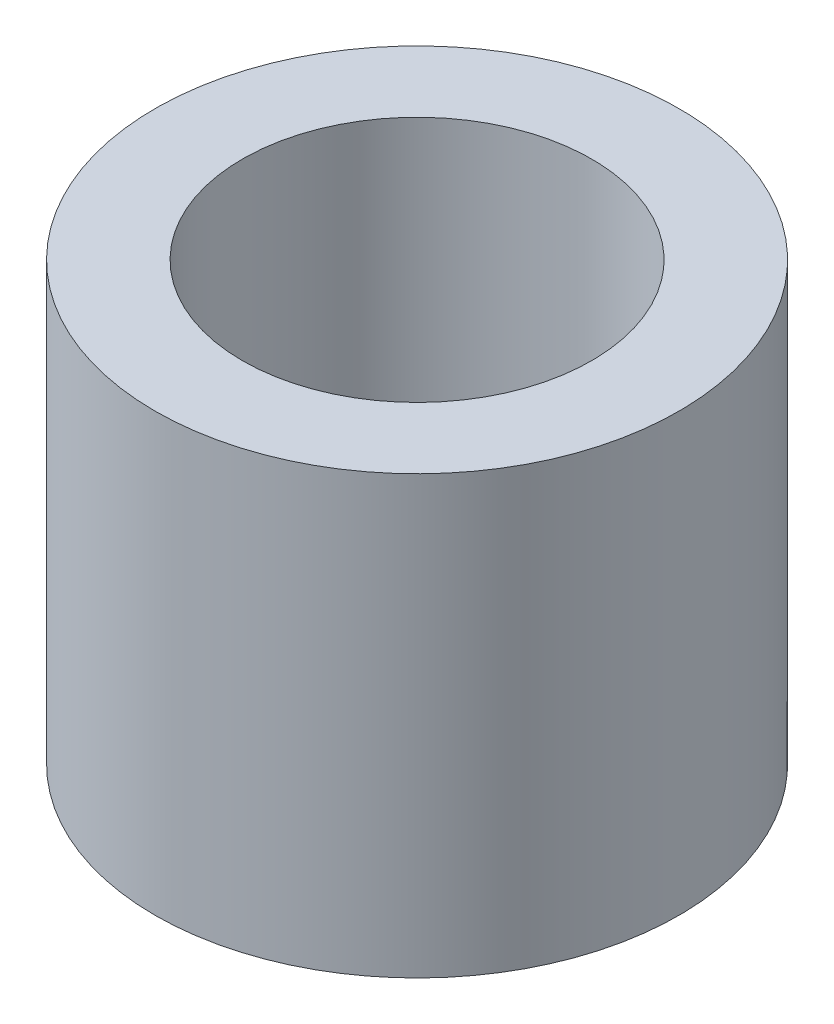
SolidWorks part; units mm, degrees
ref_plane "Płaszczyzna przednia" through (0, 0, 0) normal (0, 0, 1) x (1, 0, 0)
ref_plane "Płaszczyzna górna" through (0, 0, 0) normal (0, 1, 0) x (1, 0, 0)
ref_plane "Płaszczyzna prawa" through (0, 0, 0) normal (1, 0, 0) x (0, 0, -1)
sketch "Sketch1" plane through (0, 0, 0) normal (0, 1, 0) x (1, 0, 0)
  circle A0 centre (0, 0.2658) radius 2
  circle A1 centre (0, 0.2658) radius 3
  dimension "D1" = 4
  dimension "D2" = 6
extrude "Boss-Extrude1" add sketch "Sketch1" along normal blind 5
